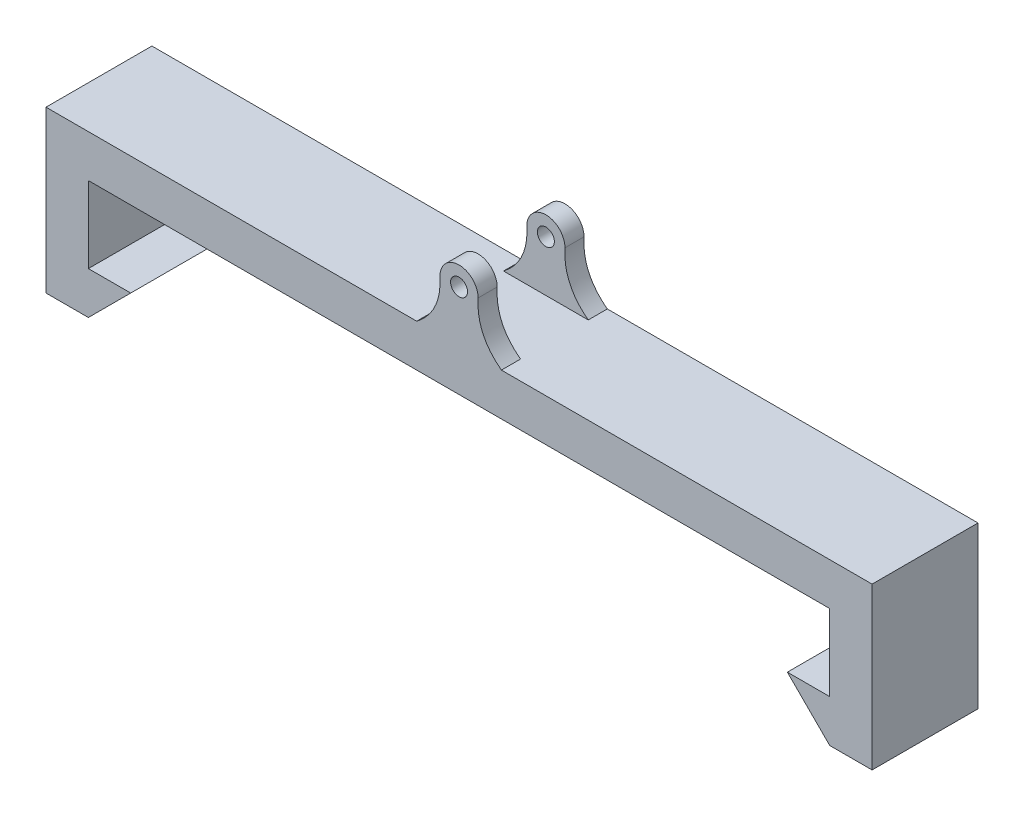
SolidWorks part; units mm, degrees
ref_plane "Plan de face" through (0, 0, 0) normal (0, 0, 1) x (1, 0, 0)
ref_plane "Plan de dessus" through (0, 0, 0) normal (0, 1, 0) x (1, 0, 0)
ref_plane "Plan de droite" through (0, 0, 0) normal (1, 0, 0) x (0, 0, -1)
sketch "Esquisse1" plane through (0, 0, 0) normal (0, 0, 1) x (1, 0, 0)
  line L0 (0, 0) -> (195, 0)
  line L1 (195, 0) -> (195, -38)
  line L2 (0, 0) -> (0, -38)
  line L3 (0, -38) -> (10, -38)
  line L4 (10, -28) -> (10, -10)
  line L5 (10, -28) -> (20, -28)
  line L6 (20, -28) -> (10, -38)
  line L7 (10, -10) -> (185, -10)
  line L8 (185, -10) -> (185, -28)
  line L9 (185, -28) -> (175, -28)
  line L10 (195, -38) -> (185, -38)
  line L11 (185, -38) -> (175, -28)
  dimension "D1" = 10
  dimension "D2" = 10
  dimension "D3" = 10
extrude "Boss.-Extru.1" add sketch "Esquisse1" along normal blind 25
sketch "Esquisse2" plane through (0, 0, 25) normal (0, 0, 1) x (1, 0, 0)
  line L2 (195, 0) -> (0, 0) construction
  line L7 (97.5, 0) -> (87.5, 0)
  line L8 (97.5, 0) -> (107.5, 0)
  circle A0 centre (97.5, 12) radius 2
  arc A1 (93, 12) -> (102, 12) centre (97.5, 12) cw
  spline S0 degree 2 poles (93, 12) (93.4735, 4.5301) (87.5, 0) knots 0 0 0 1 1 1
  spline S1 degree 2 poles (102, 12) (101.5265, 4.5301) (107.5, 0) knots 0 0 0 1 1 1
extrude "Boss.-Extru.2" add sketch "Esquisse2" against normal blind 4.5
sketch "Esquisse4" plane through (0, 0, 0) normal (0, 0, -1) x (-1, 0, 0)
  line L1 (-195, 0) -> (0, 0) construction
  line L2 (-97.5, 0) -> (-107.5, 0)
  line L3 (-97.5, 0) -> (-87.5, 0)
  circle A0 centre (-97.5, 12) radius 2
  arc A1 (-102, 12) -> (-93, 12) centre (-97.5, 12) cw
  parabola Q0 (-107.5, 0) -> (-102, 12) focus (-108.7221, 7.8375) apex (-103.1283, 5.2868) construction
  parabola Q1 (-93, 12) -> (-87.5, 0) focus (-86.2779, 7.8375) apex (-91.8717, 5.2868) construction
  spline S0 degree 2 poles (-102, 12) (-101.5278, 4.5272) (-107.5, 0) knots 0 0 0 1 1 1
  spline S1 degree 2 poles (-93, 12) (-93.4722, 4.5272) (-87.5, 0) knots 0 0 0 1 1 1
  dimension "D9" = 4.5
  dimension "D10" = 12
  dimension "D4" = 0
  dimension "D5" = 0
  dimension "D6" = 10
  dimension "D7" = 10
  dimension "D8" = 4.5
  dimension "D11" = 12
extrude "Boss.-Extru.3" add sketch "Esquisse4" against normal blind 4.5
